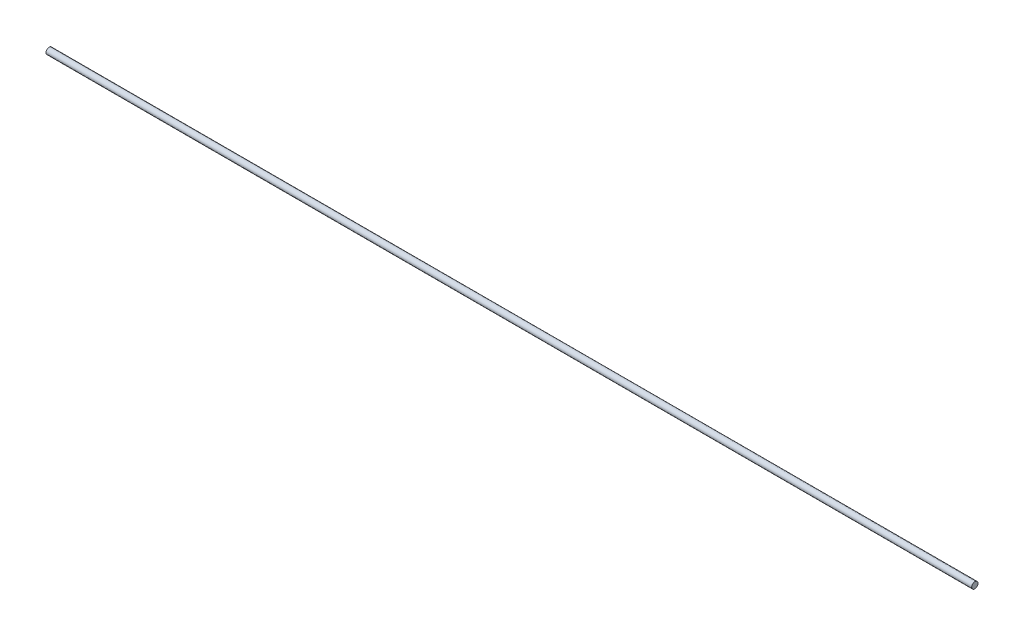
SolidWorks part; units mm, degrees
material "Glass"
ref_plane "Front Plane" through (0, 0, 0) normal (0, 0, 1) x (1, 0, 0)
ref_plane "Top Plane" through (0, 0, 0) normal (0, 1, 0) x (1, 0, 0)
ref_plane "Right Plane" through (0, 0, 0) normal (1, 0, 0) x (0, 0, -1)
sketch "Sketch1" plane through (0, 0, 0) normal (1, 0, 0) x (0, 0, -1)
  circle A0 centre (0, 0) radius 1
  dimension "D1" = 2
extrude "Boss-Extrude1" add sketch "Sketch1" along normal blind 295
